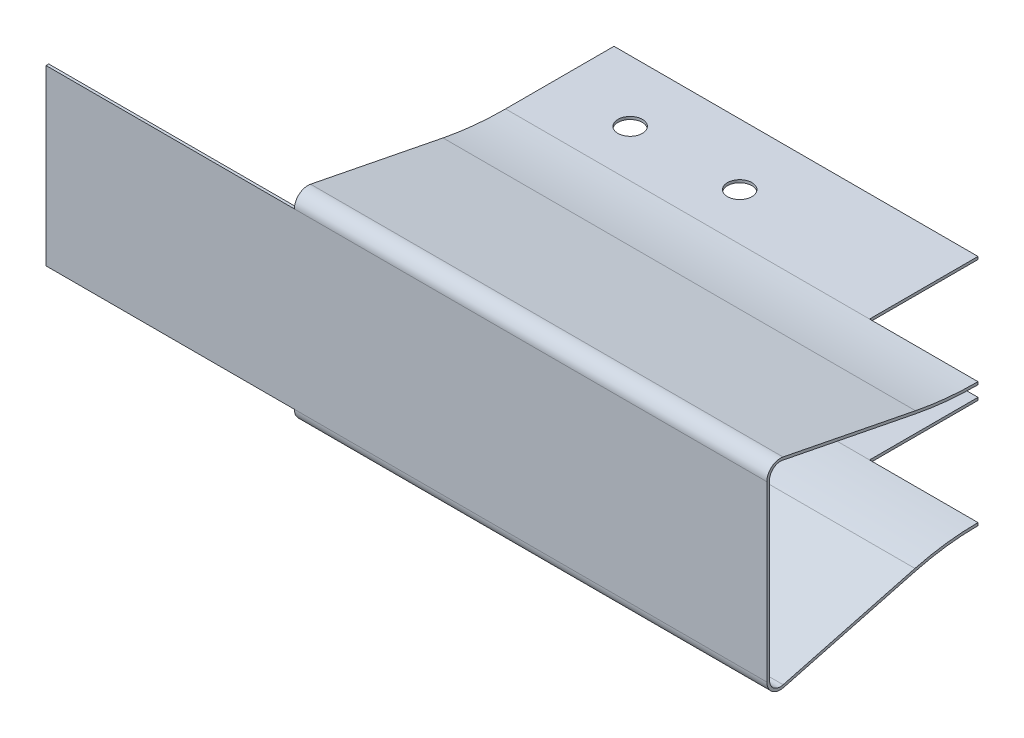
SolidWorks part; units mm, degrees
ref_plane "Front Plane" through (0, 0, 0) normal (0, 0, 1) x (1, 0, 0)
ref_plane "Top Plane" through (0, 0, 0) normal (0, 1, 0) x (1, 0, 0)
ref_plane "Right Plane" through (0, 0, 0) normal (1, 0, 0) x (0, 0, -1)
sketch "Sketch1" plane through (0, 0, 0) normal (1, 0, 0) x (0, 0, -1)
  line L0 (-14.22, 5) -> (-22.22, 5) construction
  line L1 (-24.22, 8) -> (-22.22, 8) construction
  line L2 (-24.22, 8) -> (-24.22, -8) construction
  line L3 (-24.22, -8) -> (-22.22, -8) construction
  line L4 (-14.22, 5) -> (-14.22, 3) construction
  line L5 (-24.22, 8) -> (-14.22, -5) construction
  line L6 (-24.22, -8) -> (-14.22, 5) construction
  line L7 (-22.22, 5) -> (-22.22, 8) construction
  line L8 (-14.22, 3) -> (-21.22, 3) construction
  line L9 (-21.22, 3) -> (-21.22, -3) construction
  line L10 (-21.22, -3) -> (-14.22, -3) construction
  line L11 (-14.22, -5) -> (-22.22, -5) construction
  line L12 (-22.22, -5) -> (-22.22, -8) construction
  line L13 (-14.22, -3) -> (-14.22, -5) construction
  line L14 (-24.22, 8) -> (-24.22, -8)
  line L15 (-10.8136, 6.5687) -> (-23.0262, 8.981)
  line L16 (-5, 5) -> (-5, -5) construction
  line L17 (-5, -5) -> (5, -5) construction
  line L18 (5, 5) -> (5, -5) construction
  line L19 (-5, 5) -> (5, -5) construction
  line L20 (-5, -5) -> (5, 5) construction
  line L21 (-5, 5) -> (5, 5) construction
  line L22 (-5, 5) -> (-5, 6) construction
  line L23 (-5, 6) -> (5, 6) construction
  line L24 (5, 5) -> (5, 6) construction
  line L25 (-10.8136, -5.7553) -> (-22.9645, -8.9668)
  line L26 (-5, -5) -> (5, -5)
  line L27 (-5, 6.25) -> (5, 6.25)
  line L28 (-5, 6) -> (5, 6)
  line L29 (-10.7651, 6.8139) -> (-22.9778, 9.2263)
  line L30 (-24.47, 8) -> (-24.47, -8)
  line L31 (-10.7497, -5.997) -> (-22.9006, -9.2085)
  line L32 (-5, -5.25) -> (5, -5.25)
  line L33 (5, 6.25) -> (5, 6)
  line L34 (5, -5) -> (5, -5.25)
  arc A0 (-24.22, -8) -> (-22.9645, -8.9668) centre (-23.22, -8) ccw
  arc A1 (-23.0262, 8.981) -> (-24.22, 8) centre (-23.22, 8) ccw
  arc A2 (-5, 6.25) -> (-10.7651, 6.8139) centre (-5, 36) cw
  arc A3 (-22.9778, 9.2263) -> (-24.47, 8) centre (-23.22, 8) ccw
  arc A4 (-24.47, -8) -> (-22.9006, -9.2085) centre (-23.22, -8) ccw
  arc A5 (-5, -5.25) -> (-10.7497, -5.997) centre (-5, -27.7512) ccw
  arc A6 (-5, -5) -> (-10.8136, -5.7553) centre (-5, -27.7512) ccw
  arc A7 (-5, 6) -> (-10.8136, 6.5687) centre (-5, 36) cw
  point P0 (-18.0662, 0)
  point P1 (0, 0)
  dimension "D13" = 30
  dimension "D17" = 1
  dimension "D1" = 16
  dimension "D2" = 10
  dimension "D3" = 2
  dimension "D4" = 2
  dimension "D5" = 2
  dimension "D6" = 3
  dimension "D7" = 6
  dimension "D8" = 3
  dimension "D9" = 10
  dimension "D10" = 10
  dimension "D11" = 16.22
  dimension "D12" = 1
  dimension "D14" = 0.25
extrude "Extrude1" add sketch "Sketch1" along normal mid plane 132.92
sketch "Sketch2" plane through (0, 0, 0) normal (0, 0, 1) x (1, 0, 0)
  line L0 (-22.9, 8) -> (-22.9, 9.25)
  line L1 (-22.9, 8) -> (22.9, 8)
  line L2 (-22.9, 8) -> (-22.9, -8) construction
  line L3 (-22.9, -8) -> (22.9, -8)
  line L4 (22.9, 8) -> (22.9, -8) construction
  line L5 (-22.9, 8) -> (22.9, -8) construction
  line L6 (-22.9, -8) -> (22.9, 8) construction
  line L7 (66.46, 9.25) -> (-66.46, 9.25) construction
  line L8 (-22.9, 9.25) -> (22.9, 9.25)
  line L9 (22.9, 9.25) -> (22.9, 8)
  line L10 (22.9, -8) -> (22.9, -9.25)
  line L11 (-66.46, -9.25) -> (66.46, -9.25) construction
  line L12 (22.9, -9.25) -> (-22.9, -9.25)
  line L13 (-22.9, -9.25) -> (-22.9, -8)
  point P0 (0, 0)
  dimension "D1" = 45.8
  dimension "D2" = 16
extrude "Cut-Extrude1" cut sketch "Sketch2" along normal through all
sketch "Sketch3" plane through (0, 0, 0) normal (0, 1, 0) x (1, 0, 0)
  line L0 (-22.9, -16.7696) -> (-22.9, -22.9778) construction
  line L1 (-22.9, -24.22) -> (22.9, -24.22)
  line L2 (-22.9, -24.22) -> (-22.9, 5)
  line L3 (-22.9, 5) -> (22.9, 5)
  line L4 (22.9, -24.22) -> (22.9, 5)
  line L5 (-22.9, -24.22) -> (22.9, 5) construction
  line L6 (-22.9, 5) -> (22.9, -24.22) construction
  line L7 (66.46, 5) -> (-66.46, 5) construction
  line L9 (22.9, -24.22) -> (-22.9, -24.22) construction
  point P0 (0, -9.61)
extrude "Cut-Extrude2" cut sketch "Sketch3" against normal through all and the other way through all
sketch "Sketch4" plane through (0, 0, 0) normal (0, 1, 0) x (1, 0, 0)
  line L0 (-66.46, 5) -> (-66.46, -5) construction
  line L1 (-22.9, 5) -> (-66.46, 5) construction
  line L3 (0, 0) -> (0, -20.9406) construction
  line L4 (-22.9, -5) -> (-66.46, -5) construction
  line L5 (-66.46, 5) -> (-56.46, 5)
  line L6 (-66.46, 5) -> (-66.46, -5)
  line L7 (-66.46, -5) -> (-56.46, -5)
  line L8 (-56.46, 5) -> (-56.46, -5)
  line L9 (-66.46, 5) -> (-56.46, -5) construction
  line L10 (-66.46, -5) -> (-56.46, 5) construction
  line L11 (66.46, -5) -> (56.46, 5) construction
  line L12 (66.46, 5) -> (56.46, -5) construction
  line L13 (66.46, 5) -> (56.46, 5)
  line L14 (66.46, 5) -> (66.46, -5)
  line L15 (66.46, -5) -> (56.46, -5)
  line L16 (56.46, 5) -> (56.46, -5)
  circle A0 centre (-61.46, 0) radius 1.75 construction
  circle A1 centre (-40.14, -0.65) radius 1.125
  circle A2 centre (-30.04, -0.65) radius 1.125
  circle A3 centre (30.04, -0.65) radius 1.125
  circle A4 centre (40.14, -0.65) radius 1.125
  dimension "D3" = 3.5
  dimension "D4" = 2.25
  dimension "D5" = 2.25
  dimension "D1" = 5
  dimension "D2" = 5
  dimension "D6" = 10.1
  dimension "D7" = 21.32
  dimension "D8" = 0.65
extrude "Cut-Extrude3" cut sketch "Sketch4" against normal through all and the other way through all
sketch "Sketch5" plane through (0, 0, 0) normal (0, 1, 0) x (1, 0, 0)
  line L0 (-66.46, -5) -> (-66.46, -10.7651) construction
  line L1 (-66.46, -24.47) -> (0, -24.47)
  line L2 (-66.46, -24.47) -> (-66.46, 5)
  line L3 (-66.46, 5) -> (0, 5)
  line L4 (0, -24.47) -> (0, 5)
  line L5 (-66.46, -24.47) -> (0, 5) construction
  line L6 (-66.46, 5) -> (0, -24.47) construction
  line L7 (-22.9, 5) -> (-56.46, 5) construction
  line L8 (-22.9, -24.47) -> (22.9, -24.47) construction
  point P0 (-33.23, -9.735)
extrude "Cut-Extrude4" cut sketch "Sketch5" against normal through all and the other way through all
